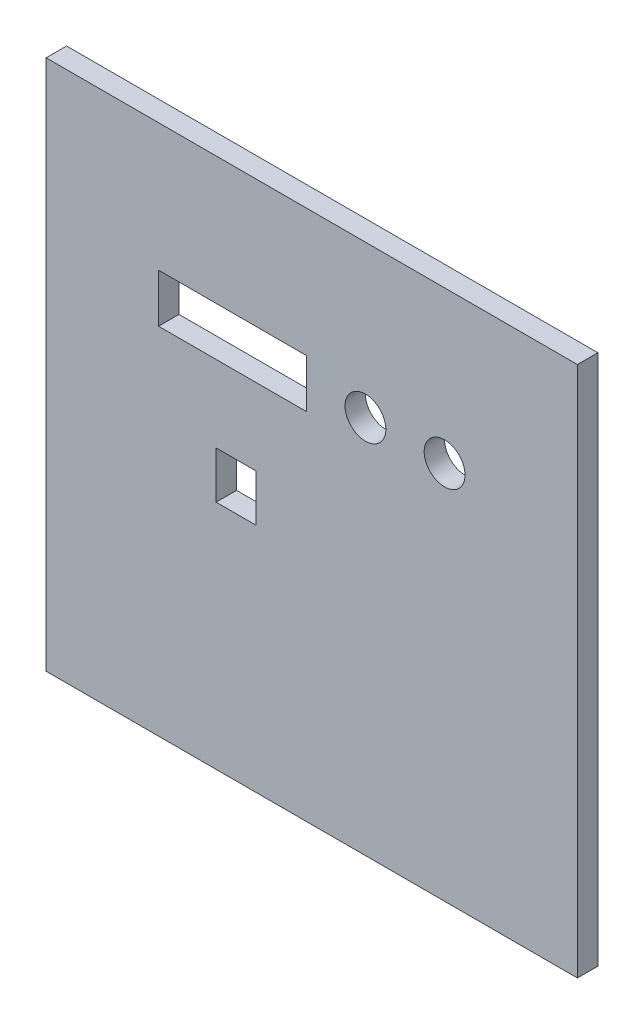
SolidWorks part; units mm, degrees
ref_plane "Front Plane" through (0, 0, 0) normal (0, 0, 1) x (1, 0, 0)
ref_plane "Top Plane" through (0, 0, 0) normal (0, 1, 0) x (1, 0, 0)
ref_plane "Right Plane" through (0, 0, 0) normal (1, 0, 0) x (0, 0, -1)
sketch "Sketch1" plane through (0, 0, 0) normal (0, 0, 1) x (1, 0, 0)
  line L1 (-132.08, 132.08) -> (132.08, 132.08)
  line L2 (-132.08, 132.08) -> (-132.08, -132.08)
  line L3 (-132.08, -132.08) -> (132.08, -132.08)
  line L4 (132.08, 132.08) -> (132.08, -132.08)
  line L5 (-132.08, 132.08) -> (132.08, -132.08) construction
  line L6 (-132.08, -132.08) -> (132.08, 132.08) construction
  point P0 (0, 0)
  dimension "D1" = 264.16
  dimension "D2" = 264.16
extrude "Boss-Extrude1" add sketch "Sketch1" along normal mid plane 10.16 contours L1 L4 L3 L2
sketch "Sketch2" plane through (0, 0, 5.08) normal (0, 0, 1) x (1, 0, 0)
  line L0 (-132.08, 132.08) -> (-132.08, -132.08) construction
  line L1 (-76.2, 68.58) -> (-2.54, 68.58)
  line L2 (-76.2, 68.58) -> (-76.2, 44.45)
  line L3 (-76.2, 44.45) -> (-2.54, 44.45)
  line L4 (-2.54, 68.58) -> (-2.54, 44.45)
  line L5 (-76.2, 68.58) -> (-2.54, 44.45) construction
  line L6 (-76.2, 44.45) -> (-2.54, 68.58) construction
  line L7 (-132.08, 132.08) -> (132.08, 132.08) construction
  line L8 (132.08, 132.08) -> (132.08, -132.08) construction
  line L10 (-47.5685, 6.35) -> (-27.7565, 6.35)
  line L11 (-47.5685, 6.35) -> (-47.5685, -17.018)
  line L12 (-47.5685, -17.018) -> (-27.7565, -17.018)
  line L13 (-27.7565, 6.35) -> (-27.7565, -17.018)
  line L14 (-47.5685, 6.35) -> (-27.7565, -17.018) construction
  line L15 (-47.5685, -17.018) -> (-27.7565, 6.35) construction
  circle A0 centre (26.67, 56.515) radius 10.16
  circle A1 centre (66.04, 56.515) radius 10.16
  point P0 (-39.37, 56.515)
  point P15 (-37.6625, -5.334)
  dimension "D5" = 20.32
  dimension "D6" = 20.32
  dimension "D9" = 19.812
  dimension "D1" = 73.66
  dimension "D2" = 24.13
  dimension "D3" = 55.88
  dimension "D4" = 63.5
  dimension "D7" = 66.04
  dimension "D8" = 29.21
  dimension "D10" = 23.368
  dimension "D11" = 38.1
extrude "Cut-Extrude1" cut sketch "Sketch2" against normal through all
